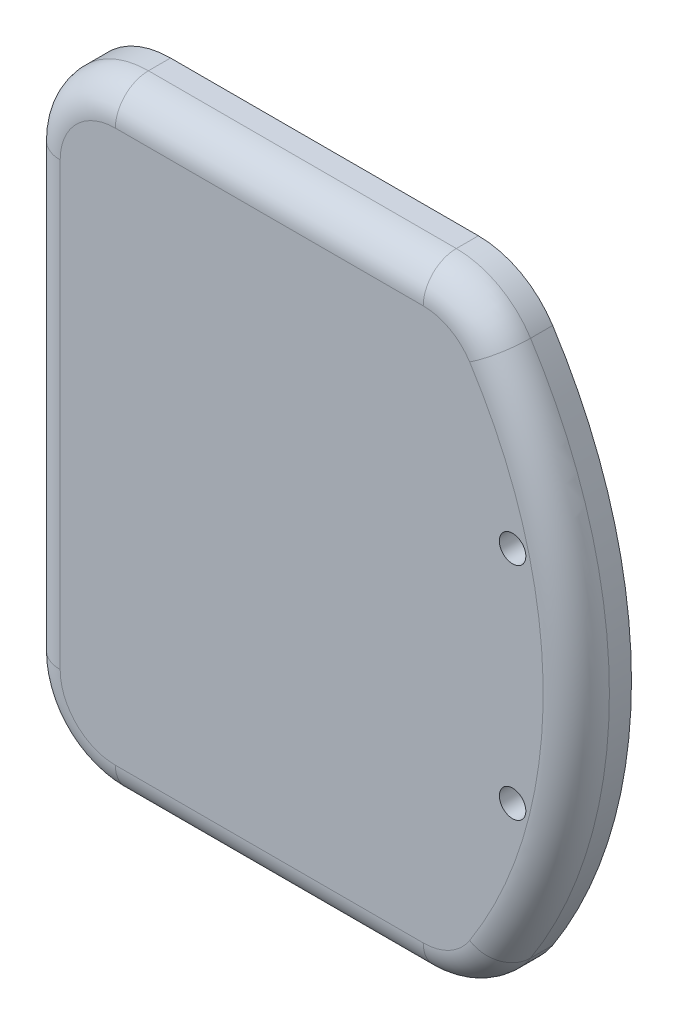
SolidWorks part; units mm, degrees
ref_plane "Спереди" through (0, 0, 0) normal (0, 0, 1) x (1, 0, 0)
ref_plane "Сверху" through (0, 0, 0) normal (0, 1, 0) x (1, 0, 0)
ref_plane "Справа" through (0, 0, 0) normal (1, 0, 0) x (0, 0, -1)
other "Configuration Table"
sketch "Эскиз1" plane through (0, 0, 0) normal (0, 0, 1) x (1, 0, 0)
  line L3 (0, 0) -> (40, 0)
  line L4 (0, 0) -> (0, 56)
  line L5 (0, 56) -> (40, 56)
  arc A5 (40, 0) -> (40, 56) centre (4.7722, 28) ccw
  dimension "D2" = 40
  dimension "D10" = 45
  dimension "D3" = 56
extrude "Бобышка-Вытянуть1" add sketch "Эскиз1" against normal blind 5
fillet "Скругление3" radius 8 4 edges at (40, 56, -2.5) (40, 0, -2.5) (0, 0, -2.5) (0, 56, -2.5)
fillet "Скругление4" radius 3 8 edges at (39.7353, 0.9788, 0) (21.9505, 0, 0) (2.3431, 2.3431, 0) (0, 28, 0) (2.3431, 53.6569, 0) (21.9505, 56, 0) (39.7353, 55.0212, 0) (49.7722, 28, 0)
hole_wizard "Отверстие с зазором M32" positions "Эскиз7" profile "Эскиз8" hole size "M2" standard "ISO"
sketch "Эскиз7" plane through (0, 0, 0) normal (0, 0, 1) x (1, 0, 0)
  circle A5 centre (44, 38) radius 1.2 construction
  circle A6 centre (44, 18) radius 1.2 construction
  point P0 (44, 38)
  point P2 (44, 18)
  point P34 (0, 0)
  point P35 (0, 0)
sketch "Эскиз8" plane through (44, 38, 0) normal (1, 0, 0) x (0, -1, 0)
  line L0 (0, 0) -> (0, 10)
  line L1 (0, 10) -> (1.2, 9.279)
  line L2 (1.2, 9.279) -> (1.2, 0)
  line L5 (1.2, 0) -> (0, 0)
  line L10 (0, 10) -> (-1.2, 9.279) construction
  line L11 (0, -6.35) -> (0, 107.95) construction
  dimension "Диаметр отверстия" = 2.4
  dimension "Глубина отверстия" = 10
  dimension "Угол заточки сверла" = 118
